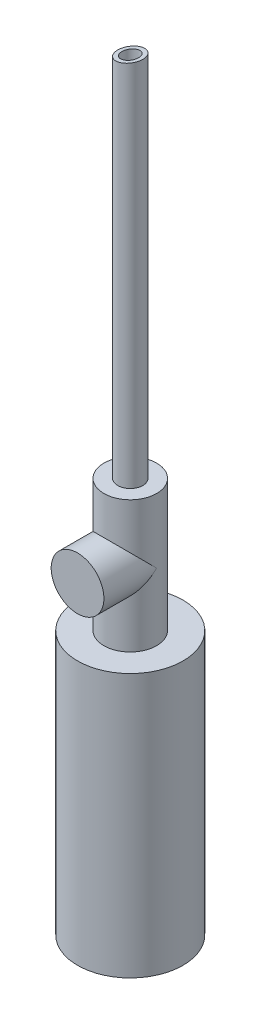
SolidWorks part; units mm, degrees
ref_plane "Alzado" through (0, 0, 0) normal (0, 0, 1) x (1, 0, 0)
ref_plane "Planta" through (0, 0, 0) normal (0, 1, 0) x (1, 0, 0)
ref_plane "Vista lateral" through (0, 0, 0) normal (1, 0, 0) x (0, 0, -1)
sketch "Croquis1" plane through (0, 0, 0) normal (0, 1, 0) x (1, 0, 0)
  circle A0 centre (0, 0) radius 1.5875
  circle A1 centre (0, 0) radius 2.3813
  dimension "D1" = 3.175
  dimension "D2" = 4.7627
extrude "Saliente-Extruir1" add sketch "Croquis1" along normal blind 70
sketch "Croquis2" plane through (0, 0, 0) normal (0, 0, 1) x (1, 0, 0)
  line L0 (2.3813, 70) -> (-2.3813, 70)
  line L1 (-2.3813, 70) -> (-2.3813, 69.1602)
  line L2 (-2.3813, 70) -> (-2.3813, 0) construction
  line L3 (-2.3813, 69.1602) -> (2.3813, 70)
  dimension "D1" = 10
extrude "Cortar-Extruir1" cut sketch "Croquis2" against normal through all both and the other way through all
sketch "Croquis3" plane through (0, 0, 0) normal (0, -1, 0) x (1, 0, 0)
  circle A0 centre (0, 0) radius 5
  circle A1 centre (0, 0) radius 1.5875
  circle A2 centre (0, 0) radius 1.5875 construction
  dimension "D1" = 10
extrude "Saliente-Extruir2" add sketch "Croquis3" along normal blind 25
sketch "Croquis4" plane through (0, -25, 0) normal (0, -1, 0) x (1, 0, 0)
  circle A0 centre (0, 0) radius 10
  circle A1 centre (0, 0) radius 1.5875
  circle A2 centre (0, 0) radius 1.5875 construction
  dimension "D1" = 20
extrude "Saliente-Extruir3" add sketch "Croquis4" along normal blind 50
sketch "Croquis5" plane through (0, 0, 0) normal (0, 0, 1) x (1, 0, 0)
  circle A0 centre (0, -12.25) radius 5
  dimension "D2" = 10
  dimension "D1" = 12.25
extrude "Saliente-Extruir4" add sketch "Croquis5" along normal blind 10
